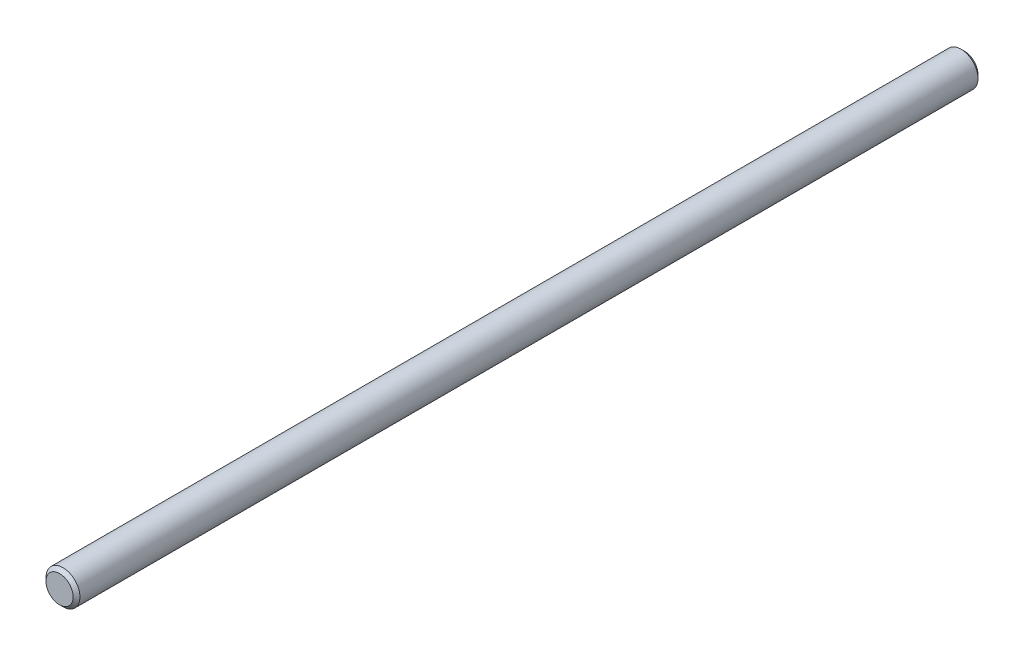
SolidWorks part; units mm, degrees
material "AISI 316 Annealed Stainless Steel Bar (SS)"
ref_plane "Front" through (0, 0, 0) normal (0, 0, 1) x (1, 0, 0)
ref_plane "Top" through (0, 0, 0) normal (0, 1, 0) x (1, 0, 0)
ref_plane "Right" through (0, 0, 0) normal (1, 0, 0) x (0, 0, -1)
sketch "Sketch1" plane through (0, 0, 0) normal (0, 0, 1) x (1, 0, 0)
  circle A0 centre (0, 0) radius 4.7625
  dimension "dia" = 9.525
extrude "Extrude1" add sketch "Sketch1" along normal mid plane 254
sketch "Sketch2" plane through (0, 0, 0) normal (1, 0, 0) x (0, 0, -1)
  point P0 (-127, 4.7625)
  point P1 (127, 4.7625)
chamfer "Chamfer1" distance 0.9525 angle 45 2 edges at (4.7625, 0, -127) (4.7625, 0, 127)
equation "\"D1@Chamfer1\" = \"dia@Sketch1\" * .1"
